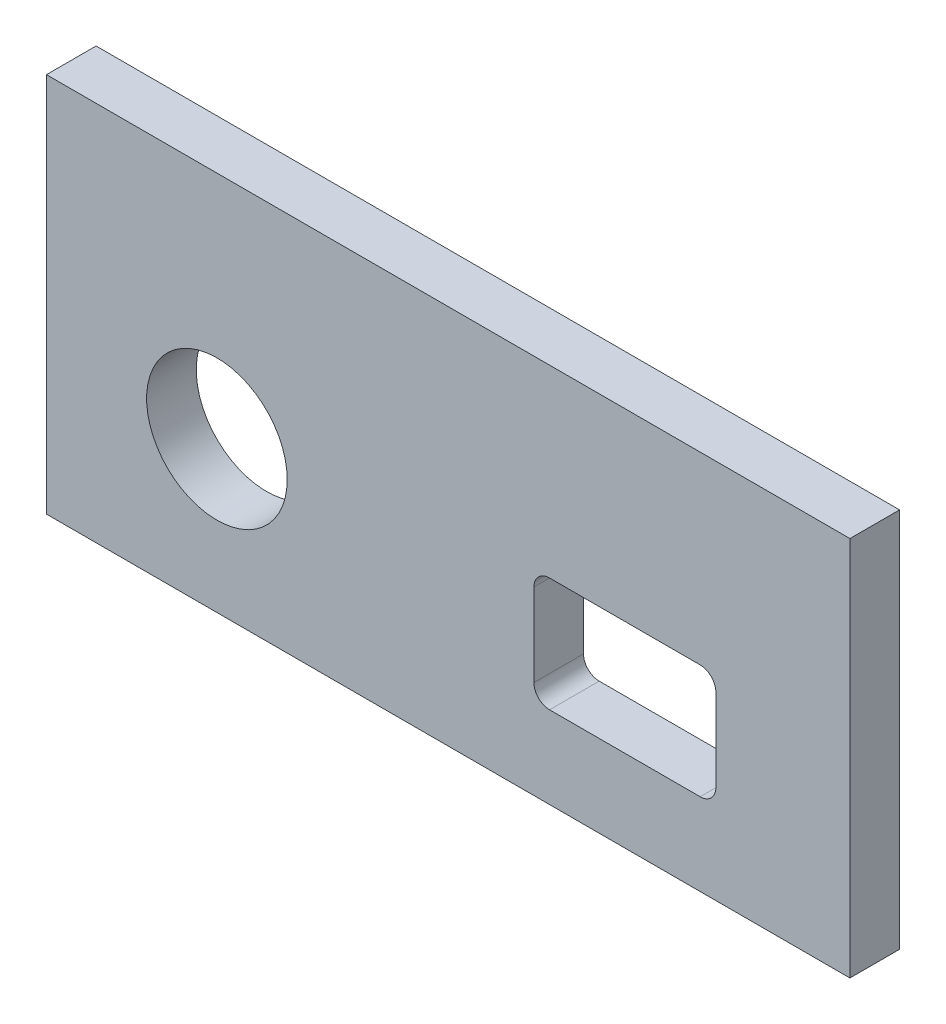
SolidWorks part; units mm, degrees
material "Acrylic (Medium-high impact)"
ref_plane "Front Plane" through (0, 0, 0) normal (0, 0, 1) x (1, 0, 0)
ref_plane "Top Plane" through (0, 0, 0) normal (0, 1, 0) x (1, 0, 0)
ref_plane "Right Plane" through (0, 0, 0) normal (1, 0, 0) x (0, 0, -1)
sketch "Sketch1" plane through (0, 0, 75.7805) normal (0, 0, 1) x (1, 0, 0)
  line L1 (8.3577, 44.8268) -> (56.9215, 44.8268)
  line L2 (8.3577, 44.8268) -> (8.3577, 21.8233)
  line L3 (8.3577, 21.8233) -> (56.9215, 21.8233)
  line L4 (56.9215, 44.8268) -> (56.9215, 21.8233)
  line L53 (37.8186, 32.7359) -> (37.8186, 27.7359)
  line L54 (38.7686, 26.7859) -> (47.8686, 26.7859)
  line L55 (48.8186, 27.7359) -> (48.8186, 32.7359)
  line L56 (47.8686, 33.6859) -> (38.7686, 33.6859)
  circle A28 centre (18.6608, 30.9068) radius 4.25
  arc A29 (37.8186, 27.7359) -> (38.7686, 26.7859) centre (38.7686, 27.7359) ccw
  arc A30 (47.8686, 26.7859) -> (48.8186, 27.7359) centre (47.8686, 27.7359) ccw
  arc A31 (48.8186, 32.7359) -> (47.8686, 33.6859) centre (47.8686, 32.7359) ccw
  arc A32 (38.7686, 33.6859) -> (37.8186, 32.7359) centre (38.7686, 32.7359) ccw
extrude "Boss-Extrude1" add sketch "Sketch1" along normal blind 3 from offset 0.25
